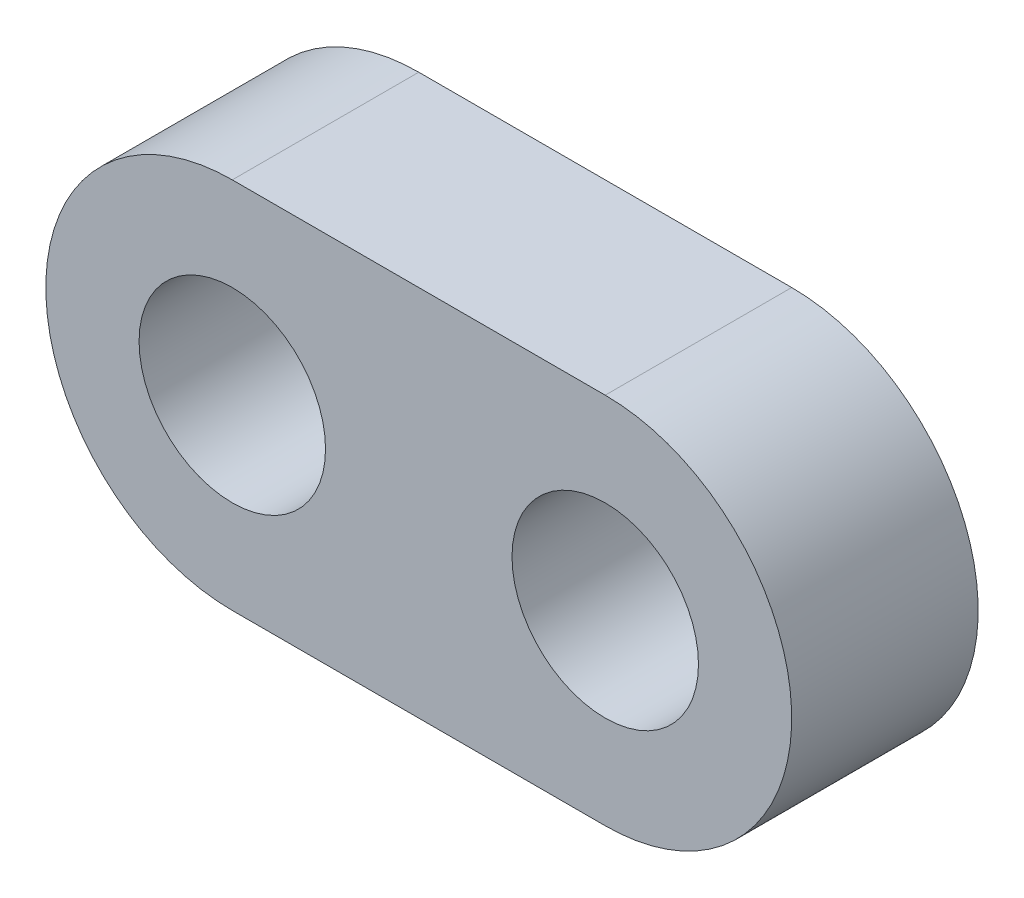
SolidWorks part; units mm, degrees
material "6061-T6 (SS)"
ref_plane "Front Plane" through (0, 0, 0) normal (0, 0, 1) x (1, 0, 0)
ref_plane "Top Plane" through (0, 0, 0) normal (0, 1, 0) x (1, 0, 0)
ref_plane "Right Plane" through (0, 0, 0) normal (1, 0, 0) x (0, 0, -1)
sketch "Sketch1" plane through (0, 0, 0) normal (0, 0, 1) x (1, 0, 0)
  line L0 (0, 6.35) -> (-12.7, 6.35)
  line L1 (-12.7, -6.35) -> (0, -6.35)
  arc A0 (0, 6.35) -> (0, -6.35) centre (0, 0) cw
  arc A1 (-12.7, 6.35) -> (-12.7, -6.35) centre (-12.7, 0) ccw
  circle A2 centre (0, 0) radius 3.175
  circle A3 centre (-12.7, 0) radius 3.175
  dimension "D1" = 6.35
  dimension "D3" = 6.35
  dimension "D2" = 12.7
extrude "Boss-Extrude1" add sketch "Sketch1" along normal blind 6.35
